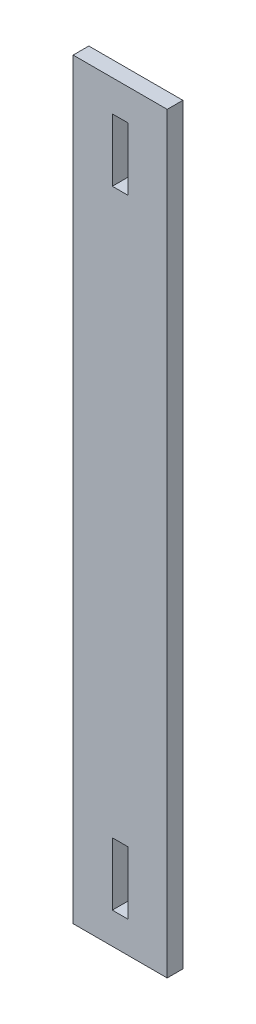
SolidWorks part; units mm, degrees
ref_plane "Front Plane" through (0, 0, 0) normal (0, 0, 1) x (1, 0, 0)
ref_plane "Top Plane" through (0, 0, 0) normal (0, 1, 0) x (1, 0, 0)
ref_plane "Right Plane" through (0, 0, 0) normal (1, 0, 0) x (0, 0, -1)
sketch "Sketch1" plane through (0, 0, 0) normal (0, 0, 1) x (1, 0, 0)
  line L1 (-19.05, -152.4) -> (19.05, -152.4)
  line L2 (-19.05, -152.4) -> (-19.05, 152.4)
  line L3 (-19.05, 152.4) -> (19.05, 152.4)
  line L4 (19.05, -152.4) -> (19.05, 152.4)
  line L5 (-19.05, -152.4) -> (19.05, 152.4) construction
  line L6 (-19.05, 152.4) -> (19.05, -152.4) construction
  point P0 (0, 0)
  dimension "D1" = 38.1
  dimension "D2" = 304.8
extrude "Boss-Extrude1" add sketch "Sketch1" along normal blind 6.35
sketch "Sketch2" plane through (0, 0, 6.35) normal (0, 0, 1) x (1, 0, 0)
  line L0 (19.05, 152.4) -> (-19.05, 152.4) construction
  line L1 (-3.175, 114.3) -> (3.175, 114.3)
  line L2 (-3.175, 114.3) -> (-3.175, 139.7)
  line L3 (-3.175, 139.7) -> (3.175, 139.7)
  line L4 (3.175, 114.3) -> (3.175, 139.7)
  line L5 (-3.175, 114.3) -> (3.175, 139.7) construction
  line L6 (-3.175, 139.7) -> (3.175, 114.3) construction
  point P0 (0, 127)
  dimension "D1" = 6.35
  dimension "D2" = 25.4
  dimension "D3" = 25.4
extrude "Cut-Extrude1" cut sketch "Sketch2" against normal through all
mirror "Mirror1" about plane through (0, 0, 0) normal (0, 1, 0) of "Cut-Extrude1"
